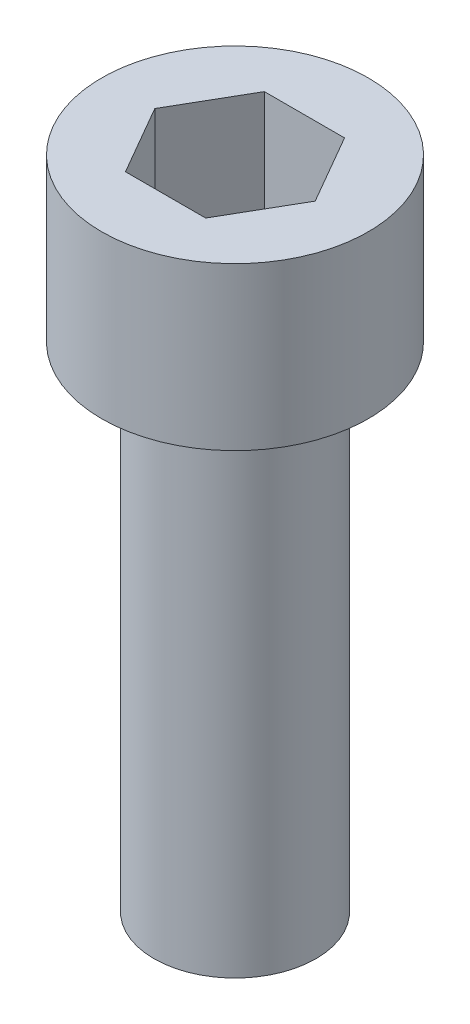
SolidWorks part; units mm, degrees
ref_plane "Front" through (0, 0, 0) normal (0, 0, 1) x (1, 0, 0)
ref_plane "Top" through (0, 0, 0) normal (0, 1, 0) x (1, 0, 0)
ref_plane "Right" through (0, 0, 0) normal (1, 0, 0) x (0, 0, -1)
sketch "profiile" plane through (0, 0, 0) normal (0, 0, 1) x (1, 0, 0)
  line L0 (0, 9.9072) -> (0, -20.7151) construction
  line L1 (0, 4.1656) -> (3.429, 4.1656)
  line L2 (3.429, 4.1656) -> (3.429, 0)
  line L3 (3.429, 0) -> (2.0828, 0)
  line L4 (2.0828, 0) -> (2.0828, -12.7)
  line L5 (2.0828, -12.7) -> (0, -12.7)
  line L6 (0, -12.7) -> (0, 4.1656)
  dimension "D1" = 6.858
  dimension "D2" = 4.1656
  dimension "thread_length" = 12.7
  dimension "D4" = 4.1656
revolve "Base-Revolve" add sketch "profiile" angle 360 about L0
sketch "Sketch1" plane through (0, 4.1656, 0) normal (0, 1, 0) x (1, 0, 0)
  line L1 (2.0622, 0) -> (1.0311, 1.7859)
  line L2 (1.0311, 1.7859) -> (-1.0311, 1.7859)
  line L3 (-1.0311, 1.7859) -> (-2.0622, 0)
  line L4 (-2.0622, 0) -> (-1.0311, -1.7859)
  line L5 (-1.0311, -1.7859) -> (1.0311, -1.7859)
  line L6 (1.0311, -1.7859) -> (2.0622, 0)
  circle A0 centre (0, 0) radius 1.7859 construction
  dimension "D1" = 3.5719
extrude "Cut-Extrude1" cut sketch "Sketch1" against normal blind 3.5719
